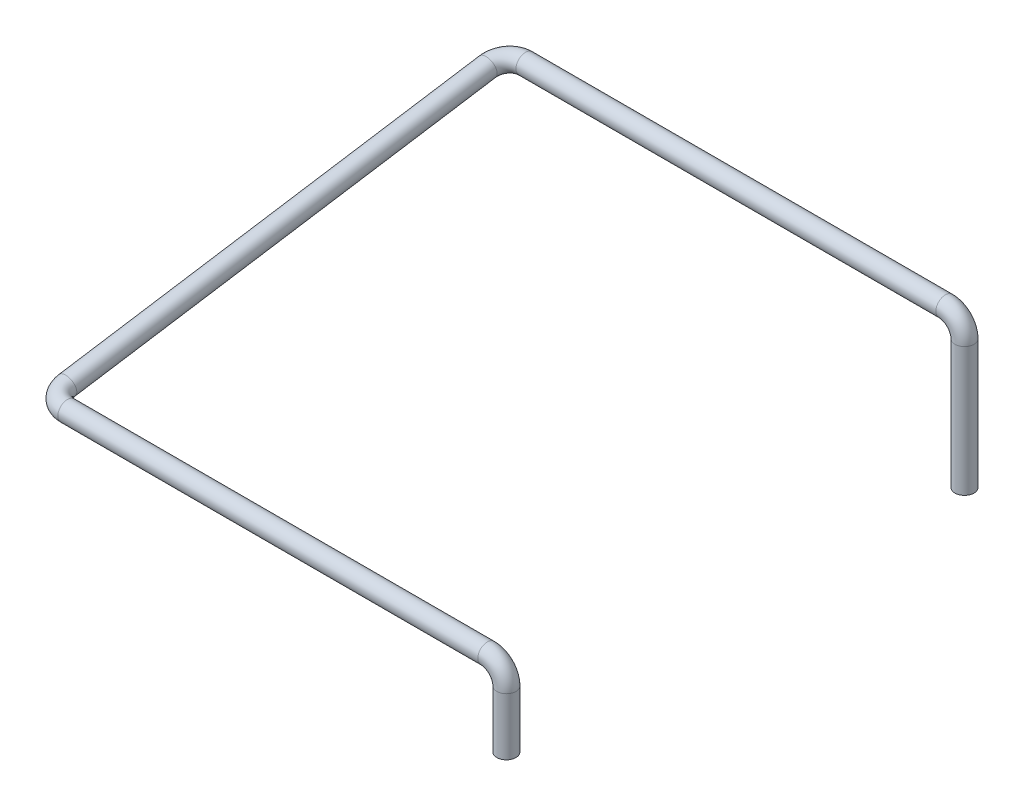
SolidWorks part; units mm, degrees
ref_plane "Front Plane" through (0, 0, 0) normal (0, 0, 1) x (1, 0, 0)
ref_plane "Top Plane" through (0, 0, 0) normal (0, 1, 0) x (1, 0, 0)
ref_plane "Right Plane" through (0, 0, 0) normal (1, 0, 0) x (0, 0, -1)
sketch "Sketch1" plane through (0, 0, 0) normal (0, 0, 1) x (1, 0, 0)
  line L0 (0, 0) -> (22, 0)
  line L1 (23, -1) -> (23, -4)
  arc A0 (22, 0) -> (23, -1) centre (22, -1) cw
  dimension "D1" = 1
  dimension "D2" = 22
  dimension "D3" = 3
ref_plane "Plane1" through (0, 0, -24) normal (0, 0, 1) x (1, 0, 0)
sketch "Sketch2" plane through (0, 0, -24) normal (0, 0, 1) x (1, 0, 0)
  line L0 (0, 3.75) -> (22, 3.75)
  line L1 (23, 2.75) -> (23, -4)
  line L2 (0, 0) -> (22, 0) construction
  arc A0 (22, 3.75) -> (23, 2.75) centre (22, 2.75) cw
  arc A1 (23, -1) -> (22, 0) centre (22, -1) ccw construction
  dimension "D1" = 3.75
ref_plane "Plane2" through (0, 0, 0) normal (0, 0.988, 0.1544) x (-1, 0, 0)
sketch "Sketch3" plane through (0, 0, 0) normal (0, 0.988, 0.1544) x (-1, 0, 0)
  line L0 (1, -1) -> (1, -23.2912)
  line L1 (0, -24.2912) -> (-22, -24.2912) construction
  line L2 (0, 0) -> (-22, 0) construction
  arc A0 (1, -23.2912) -> (0, -24.2912) centre (0, -23.2912) cw
  arc A1 (1, -1) -> (0, 0) centre (0, -1) ccw
  dimension "D1" = 1
sketch "Sketch4" plane through (0, 0, 0) normal (1, 0, 0) x (0, 0, -1)
  circle A0 centre (0, 0) radius 0.5
  dimension "D1" = 1
sweep "Sweep1" add profiles "Sketch4" path "Sketch1"
sketch "Sketch5" plane through (0, 0, 0) normal (-1, 0, 0) x (0, 0, 1)
  circle A1 centre (0, 0) radius 0.5
  circle A2 centre (0, 0) radius 0.5
  dimension "D1" = 0
sweep "Sweep2" add profiles "Sketch5" path "Sketch3"
sketch "Sketch6" plane through (0, 0, 0) normal (1, 0, 0) x (0, 0, -1)
  circle A1 centre (24, 3.75) radius 0.5
  circle A2 centre (24, 3.75) radius 0.5
  dimension "D1" = 0
sweep "Sweep3" add profiles "Sketch6" path "Sketch2"
